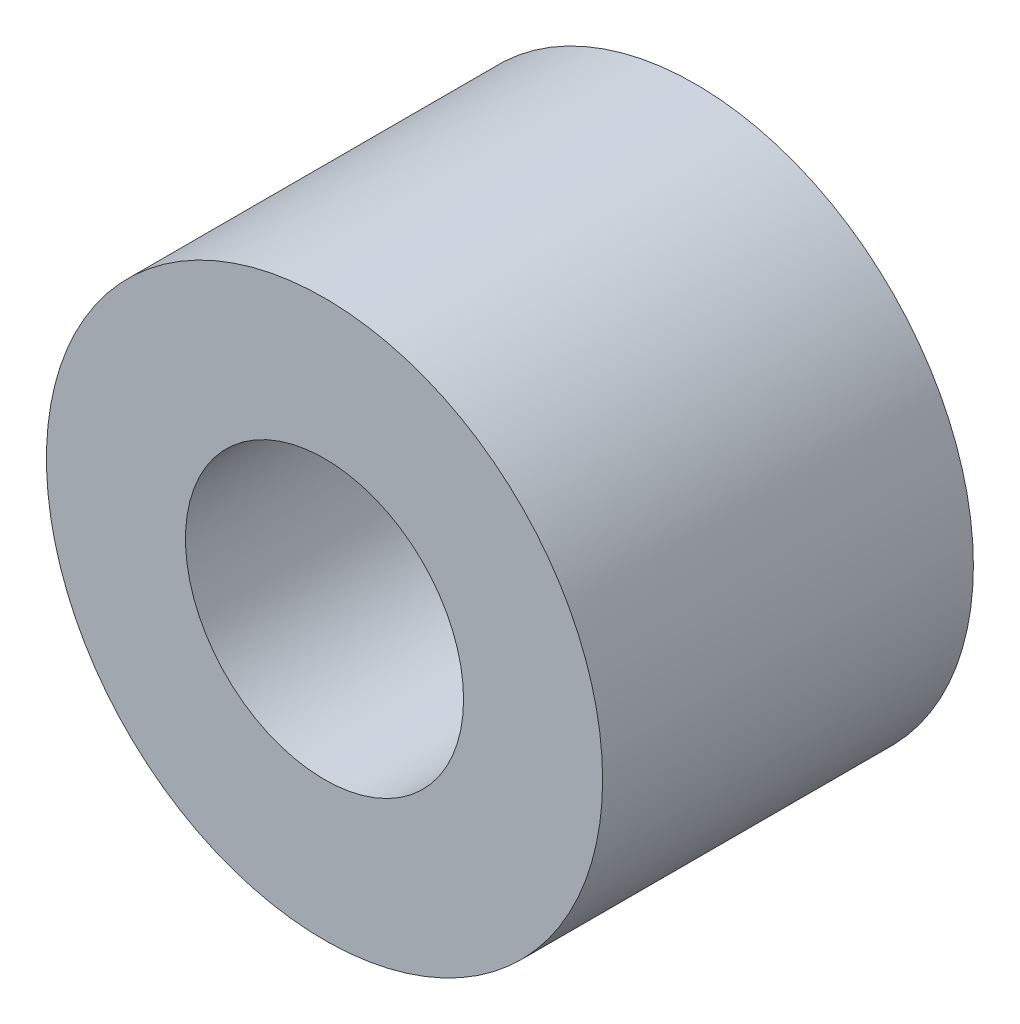
SolidWorks part; units mm, degrees
ref_plane "Front Plane" through (0, 0, 0) normal (0, 0, 1) x (1, 0, 0)
ref_plane "Top Plane" through (0, 0, 0) normal (0, 1, 0) x (1, 0, 0)
ref_plane "Right Plane" through (0, 0, 0) normal (1, 0, 0) x (0, 0, -1)
sketch "Sketch1" plane through (0, 0, 0) normal (0, 0, 1) x (1, 0, 0)
  circle A0 centre (0, 0) radius 19.05
  circle A1 centre (0, 0) radius 9.525
  dimension "OD" = 38.1
  dimension "ID" = 19.05
extrude "Extrude1" add sketch "Sketch1" along normal mid plane 25.4
sketch "Sketch2" plane through (0, 0, 0) normal (1, 0, 0) x (0, 0, -1)
  line L0 (-12.7, -9.525) -> (12.7, -9.525) construction
  line L3 (12.7, 9.525) -> (-12.7, 9.525) construction
  line L5 (-12.7, -9.525) -> (12.7, -9.525)
  line L6 (12.7, 9.525) -> (-12.7, 9.525)
sketch "Sketch4" plane through (0, 0, 12.7) normal (0, 0, 1) x (1, 0, 0)
  line L0 (0, 0) -> (-6.7352, 6.7352)
  line L1 (0, -2.1828) -> (0, 2.1828) construction
  circle A0 centre (0, 0) radius 9.525 construction
  dimension "D1" = 45
